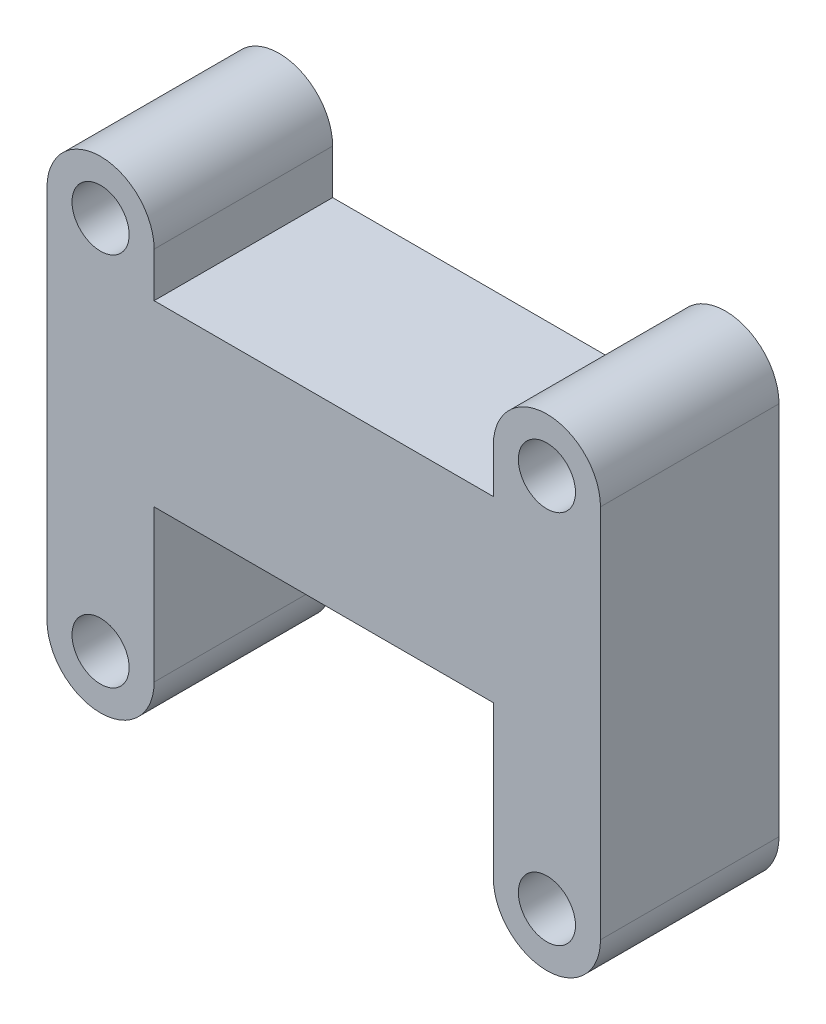
SolidWorks part; units mm, degrees
material "ABS"
ref_plane "Front Plane" through (0, 0, 0) normal (0, 0, 1) x (1, 0, 0)
ref_plane "Top Plane" through (0, 0, 0) normal (0, 1, 0) x (1, 0, 0)
ref_plane "Right Plane" through (0, 0, 0) normal (1, 0, 0) x (0, 0, -1)
sketch "Sketch1" plane through (0, 0, 0) normal (0, 0, 1) x (1, 0, 0)
  line L0 (0, 0) -> (0, 21) construction
  line L1 (-3, 0) -> (-3, 21)
  line L2 (3, 0) -> (3, 21)
  line L3 (12.5, 18.5) -> (12.5, 8.5) construction
  line L4 (25, 0) -> (25, 21) construction
  line L5 (3, 8.5) -> (22, 8.5)
  line L6 (3, 8.5) -> (3, 18.5)
  line L7 (3, 18.5) -> (22, 18.5)
  line L8 (22, 8.5) -> (22, 18.5)
  line L9 (28, 0) -> (28, 21)
  line L10 (22, 0) -> (22, 21)
  arc A0 (-3, 0) -> (3, 0) centre (0, 0) ccw
  arc A1 (3, 21) -> (-3, 21) centre (0, 21) ccw
  circle A2 centre (0, 21) radius 1.6
  circle A3 centre (0, 0) radius 1.6
  circle A4 centre (25, 0) radius 1.6
  arc A5 (28, 0) -> (22, 0) centre (25, 0) cw
  arc A6 (22, 21) -> (28, 21) centre (25, 21) cw
  circle A7 centre (25, 21) radius 1.6
  point P3 (0, 10.5)
  point P21 (25, 10.5)
  dimension "D2" = 3
  dimension "D3" = 3.2
  dimension "D1" = 21
  dimension "D4" = 10
  dimension "D5" = 19
  dimension "D6" = 8
extrude "Boss-Extrude1" add sketch "Sketch1" along normal blind 10 contours L2 A1 L1 A0 A3 A2 | L5 L8 L7 L2 | A6 L10 L8 A5 L9 A4 A7
